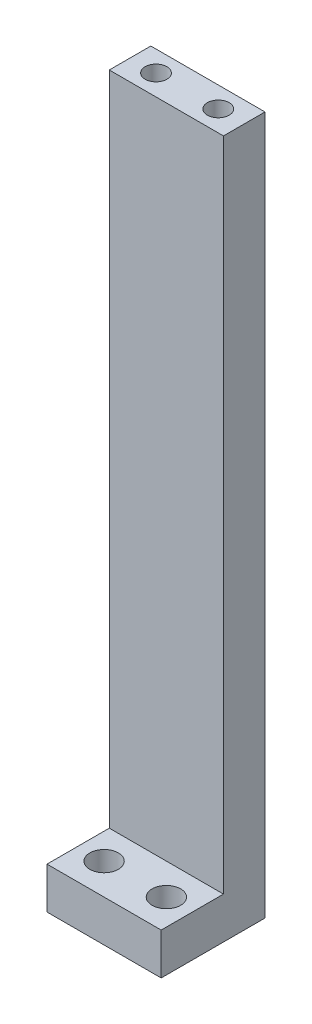
SolidWorks part; units mm, degrees
ref_plane "前视基准面" through (0, 0, 0) normal (0, 0, 1) x (1, 0, 0)
ref_plane "上视基准面" through (0, 0, 0) normal (0, 1, 0) x (1, 0, 0)
ref_plane "右视基准面" through (0, 0, 0) normal (1, 0, 0) x (0, 0, -1)
sketch "草图1" plane through (0, 0, 0) normal (0, 0, 1) x (1, 0, 0)
  line L1 (0, 0) -> (22, 0)
  line L2 (0, 0) -> (0, 134.5)
  line L3 (0, 134.5) -> (22, 134.5)
  line L4 (22, 0) -> (22, 134.5)
  dimension "D1" = 134.5
  dimension "D2" = 22
extrude "凸台-拉伸1" add sketch "草图1" along normal blind 8
hole_wizard "M5 螺纹孔1" positions "草图2" profile "草图3" tap size "M5" standard "ISO"
sketch "草图2" plane through (0, 134.5, 0) normal (0, 1, 0) x (1, 0, 0)
  point P0 (17, -4)
  point P3 (5, -4)
sketch "草图3" plane through (17, 134.5, 4) normal (1, 0, 0) x (0, 0, 1)
  line L0 (0, 0) -> (0, 13.6618)
  line L1 (0, 13.6618) -> (2.1, 12.4)
  line L2 (2.1, 12.4) -> (2.1, 0)
  line L5 (2.1, 0) -> (0, 0)
  line L10 (0, 13.6618) -> (-2.1, 12.4) construction
  line L11 (0, -6.35) -> (0, 107.95) construction
  dimension "螺纹孔钻头直径" = 4.2
  dimension "螺纹孔钻头深度" = 12.4
  dimension "导头角度" = 118
cosmetic thread "孔螺蚊线1" parameters "D1"=10, "D2"=5
cosmetic thread "孔螺蚊线2" parameters "D1"=10, "D2"=5
sketch "草图6" plane through (0, 0, 8) normal (0, 0, 1) x (1, 0, 0)
  line L0 (22, 0) -> (22, 134.5) construction
  line L1 (0, 0) -> (22, 0)
  line L2 (0, 0) -> (0, 8)
  line L3 (0, 8) -> (22, 8)
  line L4 (22, 0) -> (22, 8)
  dimension "D1" = 8
extrude "凸台-拉伸2" add sketch "草图6" along normal blind 12
sketch "草图7" plane through (0, 8, 0) normal (0, 1, 0) x (1, 0, 0)
  line L0 (0, -14) -> (22, -14) construction
  line L1 (0, -20) -> (0, -8) construction
  line L2 (22, -20) -> (22, -8) construction
  line L3 (22, -14) -> (11, -14) construction
  line L4 (11, -14) -> (11, -2.8919) construction
  circle A0 centre (5, -14) radius 2.75
  circle A1 centre (17, -14) radius 2.75
  dimension "D1" = 5.5
  dimension "D2" = 12
extrude "切除-拉伸1" cut sketch "草图7" against normal through all
